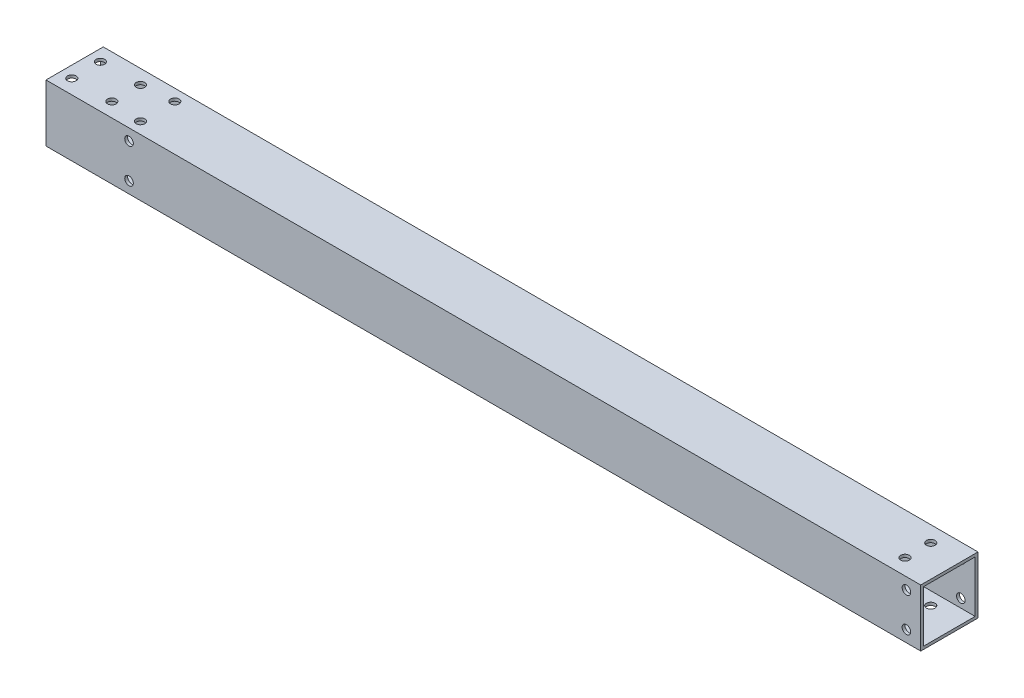
SolidWorks part; units mm, degrees
ref_plane "Front" through (0, 0, 0) normal (0, 0, 1) x (1, 0, 0)
ref_plane "Top" through (0, 0, 0) normal (0, 1, 0) x (1, 0, 0)
ref_plane "Right" through (0, 0, 0) normal (1, 0, 0) x (0, 0, -1)
sketch "草图1" plane through (0, 0, 0) normal (0, 1, 0) x (1, 0, 0)
  line L0 (0, 0) -> (305.54, 0)
  dimension "D1" = 305.54
other "铝管 20X20X1(1)"
ref_plane "基准面1" through (0, 0, 0) normal (1, 0, 0) x (0, 0, -1)
sketch "草图11" plane through (0, 0, 0) normal (1, 0, 0) x (0, 0, -1)
  line L1 (-10, -10) -> (10, -10)
  line L2 (-10, -10) -> (-10, 10)
  line L3 (-10, 10) -> (10, 10)
  line L4 (10, -10) -> (10, 10)
  line L5 (-10, -10) -> (10, 10) construction
  line L6 (-10, 10) -> (10, -10) construction
  line L7 (-9, -9) -> (9, -9)
  line L8 (-9, -9) -> (-9, 9)
  line L9 (-9, 9) -> (9, 9)
  line L10 (9, -9) -> (9, 9)
  line L11 (-9, -9) -> (9, 9) construction
  line L12 (-9, 9) -> (9, -9) construction
  point P0 (0, 0)
  point P6 (0, 0)
  point P11 (0, 0)
  dimension "D1" = 20
  dimension "D2" = 20
  dimension "D3" = 18
  dimension "D4" = 18
sketch "草图14" plane through (0, 10, 0) normal (0, 1, 0) x (1, 0, 0)
  line L0 (294.54, 10) -> (294.54, -10) construction
  line L1 (305.54, 10) -> (0, 10) construction
  line L2 (305.54, -10) -> (0, -10) construction
  line L3 (305.54, 10) -> (305.54, -10) construction
  circle A0 centre (294.54, 4.5) radius 1.5
  circle A1 centre (294.54, -4.5) radius 1.5
  dimension "D1" = 3
  dimension "D2" = 3
  dimension "D3" = 5.5
  dimension "D4" = 9
  dimension "D5" = 11
sketch "草图15" plane through (0, 10, 0) normal (0, 1, 0) x (1, 0, 0)
  line L0 (0, 0) -> (57.4874, 0) construction
  line L1 (0, 10) -> (0, -10) construction
  line L2 (305.54, 10) -> (0, 10) construction
  circle A0 centre (4, 5) radius 1.5
  circle A1 centre (4, -5) radius 1.5
  circle A2 centre (18, 5) radius 1.5
  circle A3 centre (18, -5) radius 1.5
  dimension "D1" = 3
  dimension "D2" = 3
  dimension "D3" = 4
  dimension "D4" = 5
  dimension "D5" = 10
  dimension "D7" = 14
  dimension "D6" = 2
sketch "草图16" plane through (0, 0, 10) normal (0, 0, -1) x (1, 0, 0)
  line L0 (0, 10) -> (0, -10) construction
  line L1 (305.54, -10) -> (0, -10) construction
  circle A0 centre (29, -6) radius 1.5
  circle A1 centre (29, 6) radius 1.5
  dimension "D1" = 3
  dimension "D4" = 3
  dimension "D2" = 4
  dimension "D3" = 29
  dimension "D5" = 12
extrude "切除-拉伸3" cut sketch "草图16" along normal through all
sketch "草图17" plane through (0, 0, -10) normal (0, 0, -1) x (-1, 0, 0)
  line L0 (-300.54, 10) -> (-300.54, -10) construction
  line L1 (-305.54, 10) -> (0, 10) construction
  line L2 (-305.54, -10) -> (0, -10) construction
  line L3 (-305.54, -10) -> (-305.54, 10) construction
  circle A0 centre (-300.54, 6) radius 1.5
  circle A1 centre (-300.54, -6) radius 1.5
  dimension "D1" = 3
  dimension "D2" = 3
  dimension "D3" = 4
  dimension "D4" = 4
  dimension "D5" = 5
sketch "草图18" plane through (0, 10, 0) normal (0, 1, 0) x (1, 0, 0)
  line L0 (29, 10) -> (29, -10) construction
  line L1 (305.54, 10) -> (0, 10) construction
  line L2 (305.54, -10) -> (0, -10) construction
  line L3 (0, 10) -> (0, -10) construction
  circle A0 centre (29, 6) radius 1.5
  circle A1 centre (29, -6) radius 1.5
  dimension "D2" = 3
  dimension "D3" = 3
  dimension "D1" = 29
  dimension "D4" = 4
  dimension "D5" = 12
extrude "切除-拉伸5" cut sketch "草图18" against normal through all
extrude "切除-拉伸6" cut sketch "草图14" against normal blind 20
extrude "切除-拉伸7" cut sketch "草图17" against normal blind 20
extrude "切除-拉伸8" cut sketch "草图15" against normal blind 20
